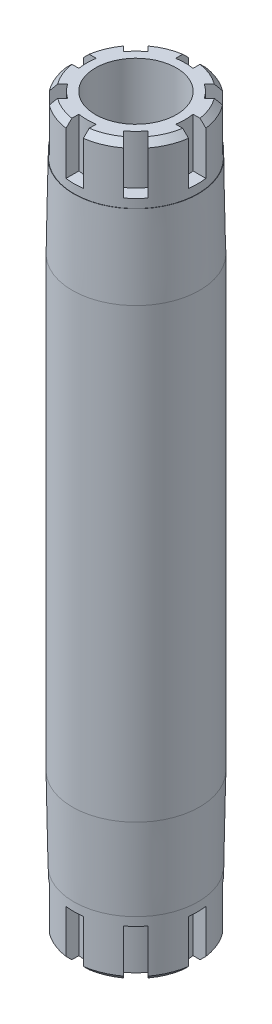
SolidWorks part; units mm, degrees
ref_plane "Plan de face" through (0, 0, 0) normal (0, 0, 1) x (1, 0, 0)
ref_plane "Plan de dessus" through (0, 0, 0) normal (0, 1, 0) x (1, 0, 0)
ref_plane "Plan de droite" through (0, 0, 0) normal (1, 0, 0) x (0, 0, -1)
sketch "Esquisse1" plane through (0, 0, 0) normal (0, 1, 0) x (1, 0, 0)
  circle A0 centre (0, 0) radius 11
  circle A1 centre (0, 0) radius 7
  dimension "D1" = 22
  dimension "D2" = 14
extrude "Extrusion1" add sketch "Esquisse1" along normal mid plane 126
sketch "Esquisse3" plane through (0, 0, 0) normal (0, 0, 1) x (1, 0, 0)
  line L0 (0, 0) -> (27.5309, 0) construction
  line L1 (0, 68.0247) -> (0, -69.0123) construction
  line L2 (10.7, 63) -> (10.7, 53)
  line L3 (11, 63) -> (-11, 63) construction
  line L4 (10.7, 53) -> (10.75, 53)
  line L5 (10.75, 53) -> (11, 38.6775)
  line L6 (11, 38.6775) -> (11, 63)
  line L7 (11, 63) -> (10.7, 63)
  line L8 (11, -63) -> (10.7, -63)
  line L9 (11, -38.6775) -> (11, -63)
  line L10 (10.75, -53) -> (11, -38.6775)
  line L11 (10.7, -53) -> (10.75, -53)
  line L12 (10.7, -63) -> (10.7, -53)
  dimension "D1" = 10
  dimension "D2" = 21.4
  dimension "D3" = 1
  dimension "D4" = 21.5
revolve "Enlèvement de matière-Révolution2" cut sketch "Esquisse3" angle 360 about L1
chamfer "Chanfrein1" distance 1 angle 45 2 edges at (0, 63, 10.7) (0, -63, 10.7)
sketch "Esquisse4" plane through (0, 63, 0) normal (0, 1, 0) x (-1, 0, 0)
  line L0 (0, 0) -> (0, -11.8773) construction
  line L1 (1.5, -10.5943) -> (1.5, -8.3666)
  line L2 (-1.5, -10.5943) -> (-1.5, -8.3666)
  arc A0 (-1.5, -8.3666) -> (1.5, -8.3666) centre (0, 0) ccw
  arc A1 (-1.5, -10.5943) -> (1.5, -10.5943) centre (0, 0) ccw
  circle A2 centre (0, 0) radius 10.7 construction
  dimension "D1" = 17
  dimension "D2" = 3
extrude "Enlèv. mat.-Extru.1" cut sketch "Esquisse4" against normal blind 8.5
pattern_circular "Répétition circulaire1" count 8 every 45 about axis through (0, 0, 0) along (0, 1, 0) of "Enlèv. mat.-Extru.1"
mirror "Symétrie1" about plane through (0, 0, 0) normal (0, 1, 0) of "Répétition circulaire1", "Enlèv. mat.-Extru.1"
